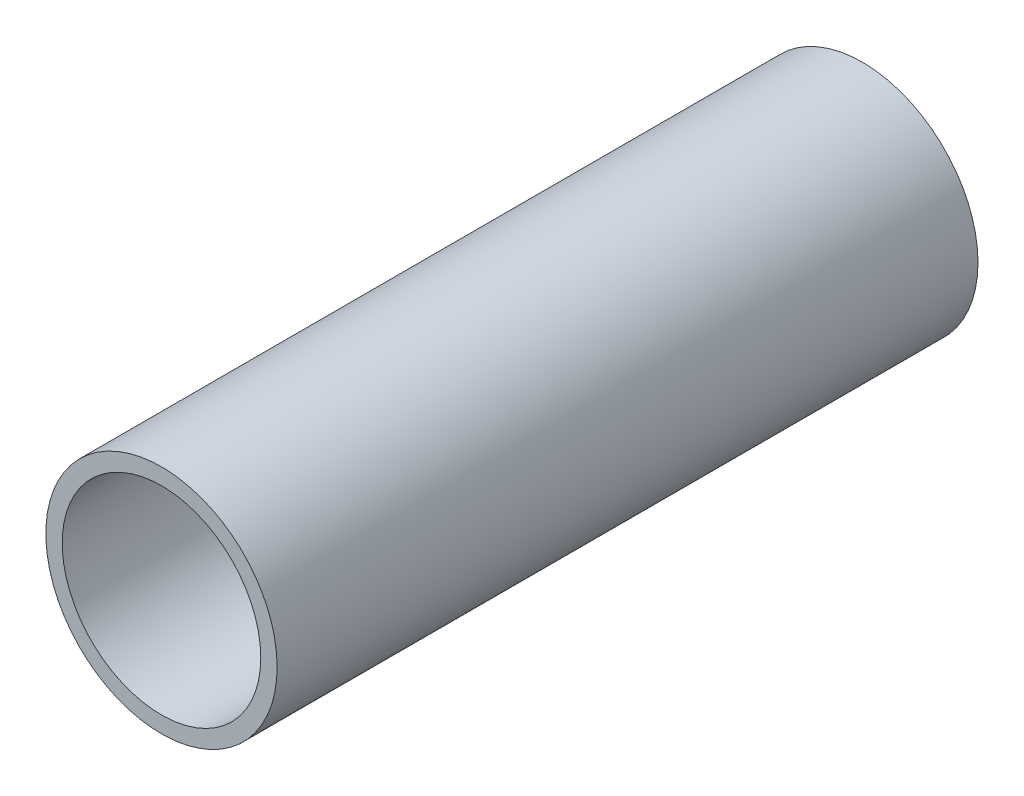
SolidWorks part; units mm, degrees
material "PVC Rigid"
ref_plane "Front Plane" through (0, 0, 0) normal (0, 0, 1) x (1, 0, 0)
ref_plane "Top Plane" through (0, 0, 0) normal (0, 1, 0) x (1, 0, 0)
ref_plane "Right Plane" through (0, 0, 0) normal (1, 0, 0) x (0, 0, -1)
sketch "Sketch1" plane through (0, 0, 0) normal (0, 0, 1) x (1, 0, 0)
  circle A1 centre (0, 0) radius 12.573
  circle A2 centre (0, 0) radius 10.795
  dimension "D1" = 25.146
  dimension "D2" = 21.59
extrude "Boss-Extrude1" add sketch "Sketch1" along normal blind 76.2
